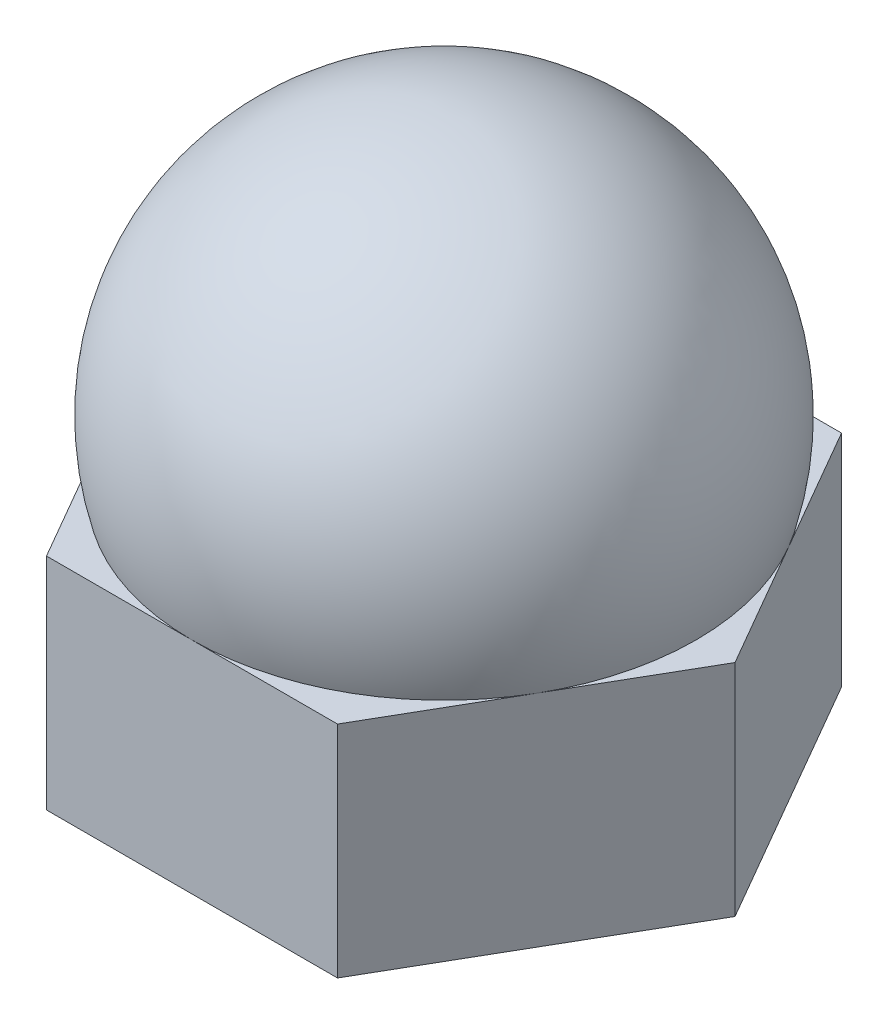
SolidWorks part; units mm, degrees
material "acero"
ref_plane "Alzado" through (0, 0, 0) normal (0, 0, 1) x (1, 0, 0)
ref_plane "Planta" through (0, 0, 0) normal (0, 1, 0) x (1, 0, 0)
ref_plane "Vista lateral" through (0, 0, 0) normal (1, 0, 0) x (0, 0, -1)
sketch "Croquis1" plane through (0, 0, 0) normal (0, 1, 0) x (1, 0, 0)
  line L1 (-1.5877, 2.75) -> (-3.1754, 0)
  line L2 (-3.1754, 0) -> (-1.5877, -2.75)
  line L3 (-1.5877, -2.75) -> (1.5877, -2.75)
  line L4 (1.5877, -2.75) -> (3.1754, 0)
  line L5 (3.1754, 0) -> (1.5877, 2.75)
  line L6 (1.5877, 2.75) -> (-1.5877, 2.75)
  circle A0 centre (0, 0) radius 2.75 construction
  circle A1 centre (0, 0) radius 1.25
  dimension "D1" = 2.5
  dimension "D2" = 5.5
extrude "Saliente-Extruir1" add sketch "Croquis1" along normal blind 2.4
sketch "Croquis3" plane through (0, 0, 0) normal (1, 0, 0) x (0, 0, -1)
  line L0 (-2.75, 0) -> (0, 0) construction
  line L1 (-2.75, 2.4) -> (2.75, 2.4)
  line L2 (0, 6) -> (0, 0) construction
  arc A0 (-2.75, 2.4) -> (2.75, 2.4) centre (0, 3.1497) cw
  point P3 (0, 6)
  dimension "D1" = 6
revolve "Revolución2" add sketch "Croquis3" angle 360 about L2
